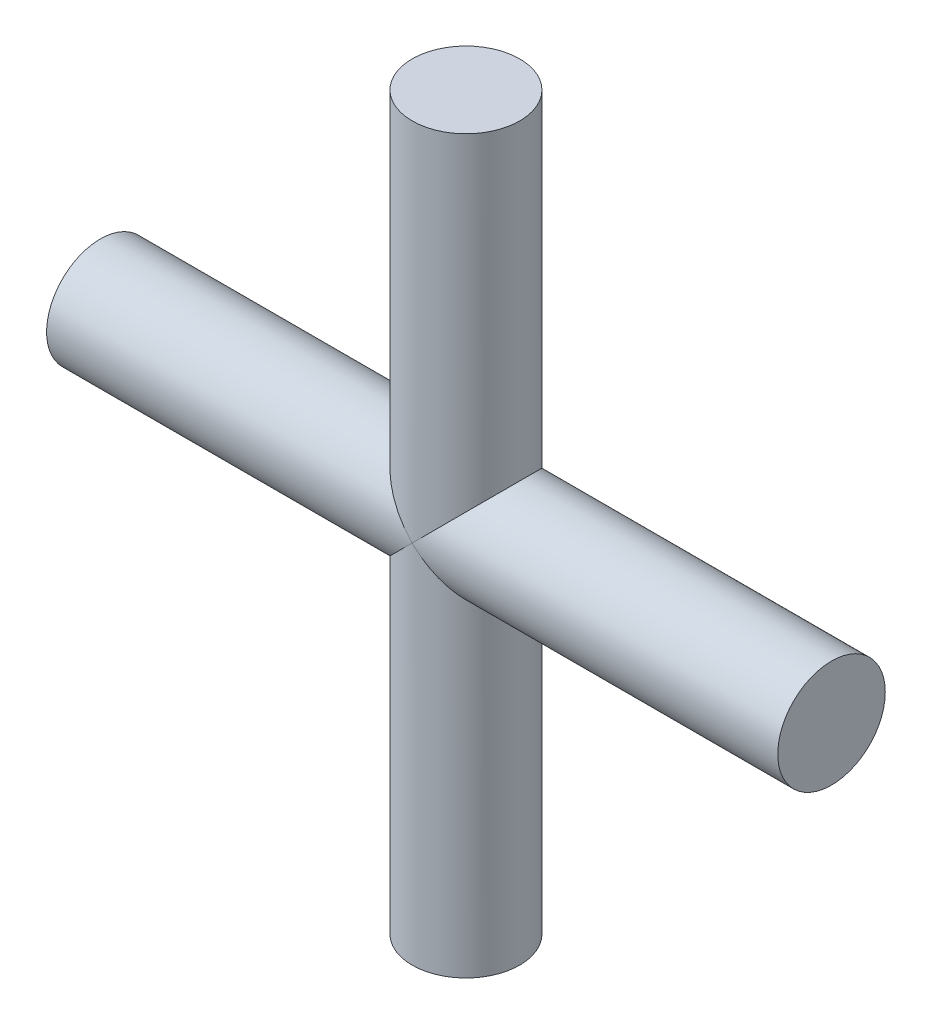
SolidWorks part; units mm, degrees
material "AISI 4340 Steel, annealed"
ref_plane "Front Plane" through (0, 0, 0) normal (0, 0, 1) x (1, 0, 0)
ref_plane "Top Plane" through (0, 0, 0) normal (0, 1, 0) x (1, 0, 0)
ref_plane "Right Plane" through (0, 0, 0) normal (1, 0, 0) x (0, 0, -1)
sketch "Sketch2" plane through (0, 0, 0) normal (0, 1, 0) x (1, 0, 0)
  circle A0 centre (0, 0) radius 2.5
  dimension "D1" = 5
extrude "Boss-Extrude1" add sketch "Sketch2" along normal blind 34
sketch "Sketch3" plane through (0, 0, 0) normal (1, 0, 0) x (0, 0, -1)
  line L0 (0, 35.8253) -> (0, -5.1073) construction
  line L1 (-2.5, 0) -> (2.5, 0) construction
  circle A0 centre (0, 17) radius 2.5
  dimension "D1" = 5
  dimension "D2" = 17
extrude "Boss-Extrude2" add sketch "Sketch3" along normal mid plane 34
